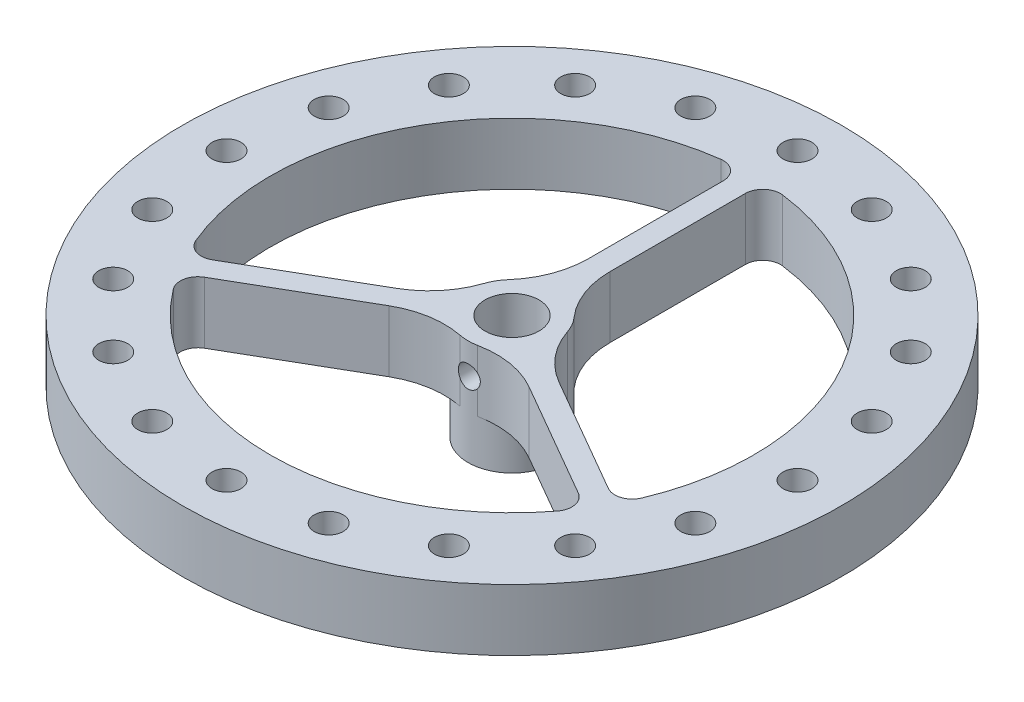
SolidWorks part; units mm, degrees
material "ABS"
ref_plane "Front Plane" through (0, 0, 0) normal (0, 0, 1) x (1, 0, 0)
ref_plane "Top Plane" through (0, 0, 0) normal (0, 1, 0) x (1, 0, 0)
ref_plane "Right Plane" through (0, 0, 0) normal (1, 0, 0) x (0, 0, -1)
sketch "Sketch1" plane through (0, 0, 0) normal (0, 1, 0) x (1, 0, 0)
  circle A0 centre (0, 0) radius 3.075
  circle A1 centre (0, 0) radius 5
  dimension "D1" = 6.15
  dimension "D2" = 10
extrude "Boss-Extrude1" add sketch "Sketch1" along normal blind 5
sketch "Sketch4" plane through (0, 0, 0) normal (0, 1, 0) x (1, 0, 0)
  circle A0 centre (0, 0) radius 27.5
  circle A1 centre (0, 0) radius 37.5
  dimension "D1" = 75
  dimension "D2" = 55
extrude "Boss-Extrude2" add sketch "Sketch4" along normal blind 5 separate body
sketch "Sketch5" plane through (0, 5, 0) normal (0, 1, 0) x (1, 0, 0)
  line L1 (-1.25, 27.5) -> (1.25, 27.5)
  line L2 (-1.25, 27.5) -> (-1.25, 4.8412)
  line L3 (-1.25, 4.8412) -> (1.25, 4.8412)
  line L4 (1.25, 27.5) -> (1.25, 4.8412)
  line L5 (-1.25, 27.5) -> (1.25, 4.8412) construction
  line L6 (-1.25, 4.8412) -> (1.25, 27.5) construction
  circle A0 centre (0, 0) radius 5 construction
  circle A2 centre (0, 0) radius 27.5 construction
  point P0 (0, 16.1706)
  point P9 (0, 27.5)
  point P10 (0, 27.5)
  dimension "D1" = 2.5
extrude "Boss-Extrude3" add sketch "Sketch5" against normal up to surface (5 mm away) up to face at (0, 0, 37.5)
pattern_circular "CirPattern1" count 3 over 360 about axis through (0, 0, 0) along (0, 1, 0) of "Boss-Extrude3"
sketch "Sketch6" plane through (0, 5, 0) normal (0, 1, 0) x (1, 0, 0)
  line L0 (1.25, 27.4716) -> (-1.25, 27.4716) construction
  line L1 (-1.25, 27.4716) -> (0, 27.4716) construction
  line L2 (0, 27.4716) -> (0, 37.5) construction
  circle A0 centre (0, 32.4858) radius 1.65
  circle A1 centre (0, 0) radius 37.5 construction
  point P5 (0, 32.4858)
  dimension "D1" = 3.3
extrude "Cut-Extrude1" cut sketch "Sketch6" against normal blind 5
fillet "Fillet1" radius 10 6 edges at (-4.8176, 2.5, 1.3381) (-1.25, 2.5, -4.8412) (1.25, 2.5, -4.8412) (4.8176, 2.5, 1.3381) (3.5676, 2.5, 3.5031) (-3.5676, 2.5, 3.5031)
fillet "Fillet2" radius 2 6 edges at (24.4161, 2.5, 12.6533) (-23.1661, 2.5, 14.8183) (23.1661, 2.5, 14.8183) (-1.25, 2.5, -27.4716) (-24.4161, 2.5, 12.6533) (1.25, 2.5, -27.4716)
pattern_circular "CirPattern2" count 20 over 360 about axis through (0, 0, 0) along (0, 1, 0) of "Cut-Extrude1"
sketch "Sketch7" plane through (0, 0, 0) normal (0, -1, 0) x (1, 0, 0)
  line L0 (11.0199, 33.9158) -> (7.9139, 33.2556)
  line L1 (0, 35.6612) -> (-2.75, 34.0735)
  line L2 (-2.75, 34.0735) -> (-2.75, 30.8981)
  line L3 (-2.75, 30.8981) -> (0, 29.3104)
  line L4 (0, 29.3104) -> (2.75, 30.8981)
  line L5 (2.75, 30.8981) -> (2.75, 34.0735)
  line L6 (2.75, 34.0735) -> (0, 35.6612)
  line L7 (7.9139, 33.2556) -> (6.9326, 30.2356)
  line L8 (6.9326, 30.2356) -> (9.0574, 27.8758)
  line L9 (9.0574, 27.8758) -> (12.1634, 28.536)
  line L10 (12.1634, 28.536) -> (13.1447, 31.556)
  line L11 (13.1447, 31.556) -> (11.0199, 33.9158)
  line L12 (20.9611, 28.8505) -> (17.8031, 29.1825)
  line L13 (17.8031, 29.1825) -> (15.9366, 26.6135)
  line L14 (15.9366, 26.6135) -> (17.2282, 23.7126)
  line L15 (17.2282, 23.7126) -> (20.3862, 23.3807)
  line L16 (20.3862, 23.3807) -> (22.2527, 25.9496)
  line L17 (22.2527, 25.9496) -> (20.9611, 28.8505)
  line L18 (28.8505, 20.9611) -> (25.9496, 22.2527)
  line L19 (25.9496, 22.2527) -> (23.3807, 20.3862)
  line L20 (23.3807, 20.3862) -> (23.7126, 17.2282)
  line L21 (23.7126, 17.2282) -> (26.6135, 15.9366)
  line L22 (26.6135, 15.9366) -> (29.1825, 17.8031)
  line L23 (29.1825, 17.8031) -> (28.8505, 20.9611)
  line L24 (33.9158, 11.0199) -> (31.556, 13.1447)
  line L25 (31.556, 13.1447) -> (28.536, 12.1634)
  line L26 (28.536, 12.1634) -> (27.8758, 9.0574)
  line L27 (27.8758, 9.0574) -> (30.2356, 6.9326)
  line L28 (30.2356, 6.9326) -> (33.2556, 7.9139)
  line L29 (33.2556, 7.9139) -> (33.9158, 11.0199)
  line L30 (35.6612, 0) -> (34.0735, 2.75)
  line L31 (34.0735, 2.75) -> (30.8981, 2.75)
  line L32 (30.8981, 2.75) -> (29.3104, 0)
  line L33 (29.3104, 0) -> (30.8981, -2.75)
  line L34 (30.8981, -2.75) -> (34.0735, -2.75)
  line L35 (34.0735, -2.75) -> (35.6612, 0)
  line L36 (33.9158, -11.0199) -> (33.2556, -7.9139)
  line L37 (33.2556, -7.9139) -> (30.2356, -6.9326)
  line L38 (30.2356, -6.9326) -> (27.8758, -9.0574)
  line L39 (27.8758, -9.0574) -> (28.536, -12.1634)
  line L40 (28.536, -12.1634) -> (31.556, -13.1447)
  line L41 (31.556, -13.1447) -> (33.9158, -11.0199)
  line L42 (28.8505, -20.9611) -> (29.1825, -17.8031)
  line L43 (29.1825, -17.8031) -> (26.6135, -15.9366)
  line L44 (26.6135, -15.9366) -> (23.7126, -17.2282)
  line L45 (23.7126, -17.2282) -> (23.3807, -20.3862)
  line L46 (23.3807, -20.3862) -> (25.9496, -22.2527)
  line L47 (25.9496, -22.2527) -> (28.8505, -20.9611)
  line L48 (20.9611, -28.8505) -> (22.2527, -25.9496)
  line L49 (22.2527, -25.9496) -> (20.3862, -23.3807)
  line L50 (20.3862, -23.3807) -> (17.2282, -23.7126)
  line L51 (17.2282, -23.7126) -> (15.9366, -26.6135)
  line L52 (15.9366, -26.6135) -> (17.8031, -29.1825)
  line L53 (17.8031, -29.1825) -> (20.9611, -28.8505)
  line L54 (11.0199, -33.9158) -> (13.1447, -31.556)
  line L55 (13.1447, -31.556) -> (12.1634, -28.536)
  line L56 (12.1634, -28.536) -> (9.0574, -27.8758)
  line L57 (9.0574, -27.8758) -> (6.9326, -30.2356)
  line L58 (6.9326, -30.2356) -> (7.9139, -33.2556)
  line L59 (7.9139, -33.2556) -> (11.0199, -33.9158)
  line L60 (0, -35.6612) -> (2.75, -34.0735)
  line L61 (2.75, -34.0735) -> (2.75, -30.8981)
  line L62 (2.75, -30.8981) -> (0, -29.3104)
  line L63 (0, -29.3104) -> (-2.75, -30.8981)
  line L64 (-2.75, -30.8981) -> (-2.75, -34.0735)
  line L65 (-2.75, -34.0735) -> (0, -35.6612)
  line L66 (-11.0199, -33.9158) -> (-7.9139, -33.2556)
  line L67 (-7.9139, -33.2556) -> (-6.9326, -30.2356)
  line L68 (-6.9326, -30.2356) -> (-9.0574, -27.8758)
  line L69 (-9.0574, -27.8758) -> (-12.1634, -28.536)
  line L70 (-12.1634, -28.536) -> (-13.1447, -31.556)
  line L71 (-13.1447, -31.556) -> (-11.0199, -33.9158)
  line L72 (-20.9611, -28.8505) -> (-17.8031, -29.1825)
  line L73 (-17.8031, -29.1825) -> (-15.9366, -26.6135)
  line L74 (-15.9366, -26.6135) -> (-17.2282, -23.7126)
  line L75 (-17.2282, -23.7126) -> (-20.3862, -23.3807)
  line L76 (-20.3862, -23.3807) -> (-22.2527, -25.9496)
  line L77 (-22.2527, -25.9496) -> (-20.9611, -28.8505)
  line L78 (-28.8505, -20.9611) -> (-25.9496, -22.2527)
  line L79 (-25.9496, -22.2527) -> (-23.3807, -20.3862)
  line L80 (-23.3807, -20.3862) -> (-23.7126, -17.2282)
  line L81 (-23.7126, -17.2282) -> (-26.6135, -15.9366)
  line L82 (-26.6135, -15.9366) -> (-29.1825, -17.8031)
  line L83 (-29.1825, -17.8031) -> (-28.8505, -20.9611)
  line L84 (-33.9158, -11.0199) -> (-31.556, -13.1447)
  line L85 (-31.556, -13.1447) -> (-28.536, -12.1634)
  line L86 (-28.536, -12.1634) -> (-27.8758, -9.0574)
  line L87 (-27.8758, -9.0574) -> (-30.2356, -6.9326)
  line L88 (-30.2356, -6.9326) -> (-33.2556, -7.9139)
  line L89 (-33.2556, -7.9139) -> (-33.9158, -11.0199)
  line L90 (-35.6612, 0) -> (-34.0735, -2.75)
  line L91 (-34.0735, -2.75) -> (-30.8981, -2.75)
  line L92 (-30.8981, -2.75) -> (-29.3104, 0)
  line L93 (-29.3104, 0) -> (-30.8981, 2.75)
  line L94 (-30.8981, 2.75) -> (-34.0735, 2.75)
  line L95 (-34.0735, 2.75) -> (-35.6612, 0)
  line L96 (-33.9158, 11.0199) -> (-33.2556, 7.9139)
  line L97 (-33.2556, 7.9139) -> (-30.2356, 6.9326)
  line L98 (-30.2356, 6.9326) -> (-27.8758, 9.0574)
  line L99 (-27.8758, 9.0574) -> (-28.536, 12.1634)
  line L100 (-28.536, 12.1634) -> (-31.556, 13.1447)
  line L101 (-31.556, 13.1447) -> (-33.9158, 11.0199)
  line L102 (-28.8505, 20.9611) -> (-29.1825, 17.8031)
  line L103 (-29.1825, 17.8031) -> (-26.6135, 15.9366)
  line L104 (-26.6135, 15.9366) -> (-23.7126, 17.2282)
  line L105 (-23.7126, 17.2282) -> (-23.3807, 20.3862)
  line L106 (-23.3807, 20.3862) -> (-25.9496, 22.2527)
  line L107 (-25.9496, 22.2527) -> (-28.8505, 20.9611)
  line L108 (-20.9611, 28.8505) -> (-22.2527, 25.9496)
  line L109 (-22.2527, 25.9496) -> (-20.3862, 23.3807)
  line L110 (-20.3862, 23.3807) -> (-17.2282, 23.7126)
  line L111 (-17.2282, 23.7126) -> (-15.9366, 26.6135)
  line L112 (-15.9366, 26.6135) -> (-17.8031, 29.1825)
  line L113 (-17.8031, 29.1825) -> (-20.9611, 28.8505)
  line L114 (-11.0199, 33.9158) -> (-13.1447, 31.556)
  line L115 (-13.1447, 31.556) -> (-12.1634, 28.536)
  line L116 (-12.1634, 28.536) -> (-9.0574, 27.8758)
  line L117 (-9.0574, 27.8758) -> (-6.9326, 30.2356)
  line L118 (-6.9326, 30.2356) -> (-7.9139, 33.2556)
  line L119 (-7.9139, 33.2556) -> (-11.0199, 33.9158)
  circle A0 centre (0, 32.4858) radius 2.75 construction
  circle A2 centre (0, 0) radius 37.5
  circle A3 centre (0, 0) radius 37.5
  point P129 (0, 0)
  dimension "D1" = 5.5
  dimension "D2" = 0
  dimension "D3" = 20
extrude "Boss-Extrude4" add sketch "Sketch7" along normal blind 2
sketch "Sketch8" plane through (0, 0, 0) normal (0, 1, 0) x (1, 0, 0)
  line L0 (-1.25, 9.9216) -> (-1.25, 25.292) construction
  line L1 (-22.5286, -11.5635) -> (-9.2173, -3.8783) construction
  line L4 (-7.9673, -6.0433) -> (-21.2786, -13.7286) construction
  line L5 (21.2786, -13.7286) -> (7.9673, -6.0433) construction
  line L6 (-1.25, 9.9216) -> (-1.25, 25.292)
  line L7 (-22.5286, -11.5635) -> (-9.2173, -3.8783)
  line L10 (-7.9673, -6.0433) -> (-21.2786, -13.7286)
  line L11 (21.2786, -13.7286) -> (7.9673, -6.0433)
  line L14 (1.25, 25.292) -> (1.25, 9.9216)
  line L15 (9.2173, -3.8783) -> (22.5286, -11.5635)
  line L16 (1.25, 25.292) -> (1.25, 9.9216)
  line L17 (9.2173, -3.8783) -> (22.5286, -11.5635)
  arc A0 (-1.25, 25.292) -> (-3.5049, 27.2757) centre (-3.25, 25.292) ccw construction
  arc A1 (-3.5049, 27.2757) -> (-25.3739, -10.6025) centre (0, 0) ccw construction
  arc A2 (-25.3739, -10.6025) -> (-22.5286, -11.5635) centre (-23.5286, -9.8314) ccw construction
  arc A9 (-21.2786, -13.7286) -> (-21.869, -16.6732) centre (-20.2786, -15.4606) ccw construction
  arc A10 (-21.869, -16.6732) -> (21.869, -16.6732) centre (0, 0) ccw construction
  arc A11 (21.869, -16.6732) -> (21.2786, -13.7286) centre (20.2786, -15.4606) ccw construction
  arc A14 (-1.25, 25.292) -> (-3.5049, 27.2757) centre (-3.25, 25.292) ccw
  arc A15 (-3.5049, 27.2757) -> (-25.3739, -10.6025) centre (0, 0) ccw
  arc A16 (-25.3739, -10.6025) -> (-22.5286, -11.5635) centre (-23.5286, -9.8314) ccw
  arc A23 (-21.2786, -13.7286) -> (-21.869, -16.6732) centre (-20.2786, -15.4606) ccw
  arc A24 (-21.869, -16.6732) -> (21.869, -16.6732) centre (0, 0) ccw
  arc A25 (21.869, -16.6732) -> (21.2786, -13.7286) centre (20.2786, -15.4606) ccw
  circle A29 centre (0, 0) radius 3.075
  circle A30 centre (0, 0) radius 3.075
  arc A32 (7.9673, -6.0433) -> (0.9891, -4.9012) centre (2.9673, -14.7036) ccw construction
  arc A33 (-3.75, 3.3072) -> (-1.25, 9.9216) centre (-11.25, 9.9216) ccw construction
  arc A34 (-3.75, 3.3072) -> (-4.7391, 1.594) centre (0, 0) ccw construction
  arc A35 (1.25, 9.9216) -> (3.75, 3.3072) centre (11.25, 9.9216) ccw
  arc A36 (4.7391, 1.594) -> (9.2173, -3.8783) centre (14.2173, 4.782) ccw
  arc A37 (22.5286, -11.5635) -> (25.3739, -10.6025) centre (23.5286, -9.8314) ccw
  arc A38 (25.3739, -10.6025) -> (3.5049, 27.2757) centre (0, 0) ccw
  arc A39 (3.5049, 27.2757) -> (1.25, 25.292) centre (3.25, 25.292) ccw
  arc A40 (1.25, 9.9216) -> (3.75, 3.3072) centre (11.25, 9.9216) ccw
  arc A41 (4.7391, 1.594) -> (9.2173, -3.8783) centre (14.2173, 4.782) ccw
  arc A42 (22.5286, -11.5635) -> (25.3739, -10.6025) centre (23.5286, -9.8314) ccw
  arc A43 (25.3739, -10.6025) -> (3.5049, 27.2757) centre (0, 0) ccw
  arc A44 (3.5049, 27.2757) -> (1.25, 25.292) centre (3.25, 25.292) ccw
  arc A45 (-9.2173, -3.8783) -> (-4.7391, 1.594) centre (-14.2173, 4.782) ccw construction
  arc A46 (4.7391, 1.594) -> (3.75, 3.3072) centre (0, 0) ccw
  arc A47 (4.7391, 1.594) -> (3.75, 3.3072) centre (0, 0) ccw
  arc A48 (-0.9891, -4.9012) -> (-7.9673, -6.0433) centre (-2.9673, -14.7036) ccw construction
  arc A49 (-0.9891, -4.9012) -> (0.9891, -4.9012) centre (0, 0) ccw construction
  arc A50 (-3.75, 3.3072) -> (-1.25, 9.9216) centre (-11.25, 9.9216) ccw
  arc A51 (-3.75, 3.3072) -> (-4.7391, 1.594) centre (0, 0) ccw
  arc A52 (-9.2173, -3.8783) -> (-4.7391, 1.594) centre (-14.2173, 4.782) ccw
  arc A53 (-0.9891, -4.9012) -> (-7.9673, -6.0433) centre (-2.9673, -14.7036) ccw
  arc A54 (7.9673, -6.0433) -> (0.9891, -4.9012) centre (2.9673, -14.7036) ccw
  arc A55 (-0.9891, -4.9012) -> (0.9891, -4.9012) centre (0, 0) ccw
  dimension "D1" = 0
  dimension "D2" = 0
extrude "Cut-Extrude2" cut sketch "Sketch8" against normal blind 3
sketch "Sketch9" plane through (0, 0, 0) normal (0, 0, 1) x (1, 0, 0)
  line L0 (15.2163, 1.4787) -> (-14.8181, 1.4787) construction
  line L1 (0, 5) -> (0, -2) construction
  line L2 (0.9891, 5) -> (-0.9891, 5) construction
  line L3 (-37.5, -2) -> (37.5, -2) construction
  circle A0 centre (0, 1.5) radius 1.25
  dimension "D1" = 2.5
extrude "Cut-Extrude3" cut sketch "Sketch9" along normal blind 10
sketch "Sketch10" plane through (0, -2, 0) normal (0, -1, 0) x (1, 0, 0)
  circle A0 centre (0, 0) radius 3.075 construction
  circle A1 centre (0, 0) radius 3.075
  circle A3 centre (0, 0) radius 5
  dimension "D1" = 10
extrude "Boss-Extrude5" add sketch "Sketch10" along normal blind 5
